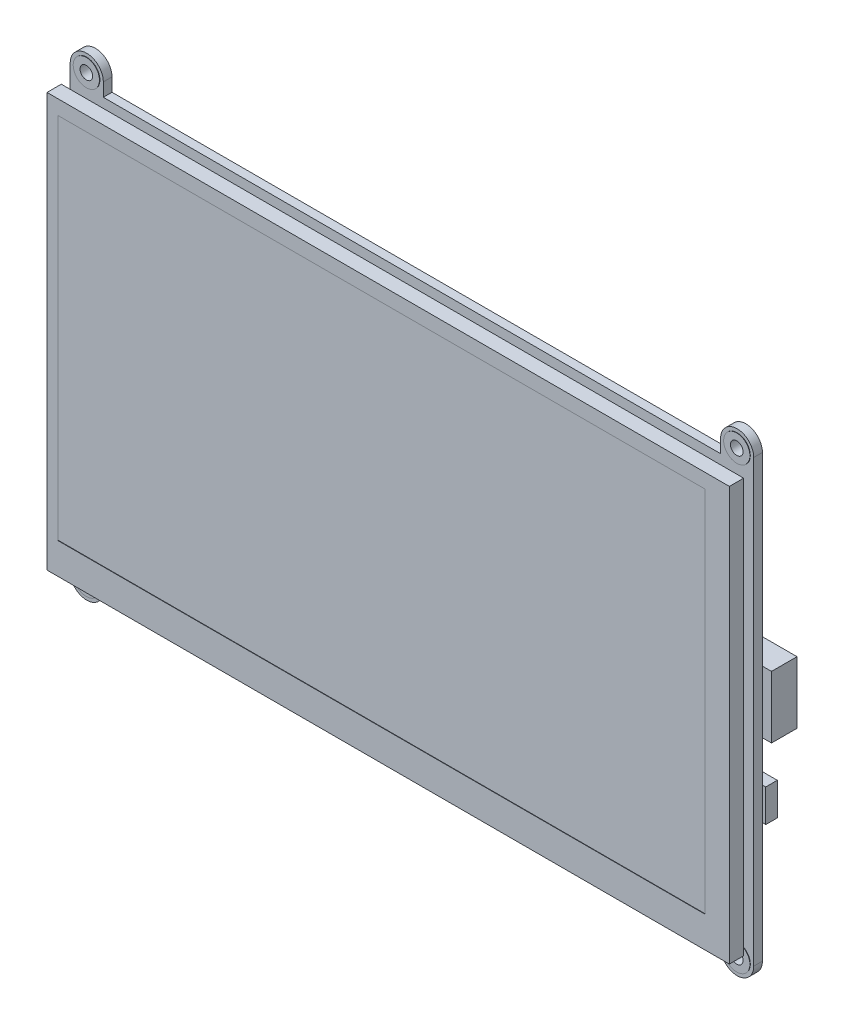
SolidWorks part; units mm, degrees
ref_plane "Plan de face" through (0, 0, 0) normal (0, 0, 1) x (1, 0, 0)
ref_plane "Plan de dessus" through (0, 0, 0) normal (0, 1, 0) x (1, 0, 0)
ref_plane "Plan de droite" through (0, 0, 0) normal (1, 0, 0) x (0, 0, -1)
sketch "Esquisse1" plane through (0, 0, 0) normal (0, 0, 1) x (1, 0, 0)
  line L0 (82.615, 53.25) -> (-82.615, -53.25) construction
  line L1 (0, 50.0368) -> (0, -50.0368) construction
  line L2 (-82.615, 53.25) -> (-82.615, -53.25)
  line L3 (-74.611, 50.0368) -> (74.611, 50.0368)
  line L4 (82.615, 53.25) -> (82.615, -53.25)
  line L5 (-78.613, 50.0368) -> (-78.613, 53.25) construction
  line L7 (-74.611, 50.0368) -> (-74.611, 53.25)
  line L8 (78.613, 50.0368) -> (78.613, 53.25) construction
  line L9 (74.611, 50.0368) -> (74.611, 53.25)
  line L11 (78.613, -50.0368) -> (78.613, -53.25) construction
  line L13 (74.611, -50.0368) -> (74.611, -53.25)
  line L14 (-78.613, -50.0368) -> (-78.613, -53.25) construction
  line L15 (-74.611, -50.0368) -> (-74.611, -53.25)
  line L17 (-74.611, -50.0368) -> (74.611, -50.0368)
  circle A0 centre (-78.613, 53.25) radius 1.524
  arc A1 (-74.611, 53.25) -> (-82.615, 53.25) centre (-78.613, 53.25) ccw
  circle A2 centre (-78.613, -53.25) radius 1.524
  arc A3 (82.615, 53.25) -> (74.611, 53.25) centre (78.613, 53.25) ccw
  circle A4 centre (78.613, -53.25) radius 1.524
  arc A5 (74.611, -53.25) -> (82.615, -53.25) centre (78.613, -53.25) ccw
  circle A6 centre (78.613, 53.25) radius 1.524
  arc A7 (-82.615, -53.25) -> (-74.611, -53.25) centre (-78.613, -53.25) ccw
  point P7 (-78.613, 53.25)
  point P12 (78.613, 51.625)
  point P21 (78.613, -51.625)
  point P28 (-78.613, -51.625)
  dimension "D5" = 3.048
  dimension "D1" = 100.0736
  dimension "D2" = 165.23
  dimension "D3" = 106.5
  dimension "D4" = 157.226
extrude "Boss.-Extru.1" add sketch "Esquisse1" along normal blind 2.1
sketch "Esquisse2" plane through (0, 0, 2.1) normal (0, 0, 1) x (1, 0, 0)
  line L0 (-74.5, 40) -> (74.5, -40) construction
  line L1 (-74.5, 40) -> (-49.1, 40)
  line L2 (-74.5, 40) -> (-74.5, 14.6)
  line L3 (-74.5, 14.6) -> (-49.1, 14.6)
  line L4 (-49.1, 40) -> (-49.1, 14.6)
  line L5 (-74.5, -14.6) -> (-49.1, -14.6)
  line L6 (-74.5, -14.6) -> (-74.5, -40)
  line L7 (-74.5, -40) -> (-49.1, -40)
  line L8 (-49.1, -14.6) -> (-49.1, -40)
  line L9 (49.1, 40) -> (74.5, 40)
  line L10 (49.1, 40) -> (49.1, 14.6)
  line L11 (49.1, 14.6) -> (74.5, 14.6)
  line L12 (74.5, 40) -> (74.5, 14.6)
  line L13 (49.1, -14.6) -> (74.5, -14.6)
  line L14 (49.1, -14.6) -> (49.1, -40)
  line L15 (49.1, -40) -> (74.5, -40)
  line L16 (74.5, -14.6) -> (74.5, -40)
  line L17 (-74.5, -40) -> (74.5, 40) construction
  dimension "D1" = 25.4
  dimension "D2" = 149
  dimension "D3" = 80
extrude "Boss.-Extru.2" add sketch "Esquisse2" along normal blind 2.3
sketch "Esquisse3" plane through (0, 0, 4.4) normal (0, 0, 1) x (1, 0, 0)
  line L1 (82.475, -50) -> (-82.475, -50)
  line L2 (82.475, -50) -> (82.475, 50)
  line L3 (82.475, 50) -> (-82.475, 50)
  line L4 (-82.475, -50) -> (-82.475, 50)
  line L5 (82.475, -50) -> (-82.475, 50) construction
  line L6 (82.475, 50) -> (-82.475, -50) construction
  point P0 (0, 0)
  dimension "D1" = 100
  dimension "D2" = 164.95
extrude "Boss.-Extru.3" add sketch "Esquisse3" along normal blind 3.45
sketch "Esquisse4" plane through (0, 0, 7.85) normal (0, 0, 1) x (1, 0, 0)
  line L0 (-82.475, 50) -> (-82.475, -50) construction
  line L1 (-79.855, 46.5) -> (76.645, 46.5)
  line L2 (-79.855, 46.5) -> (-79.855, -42.5)
  line L3 (-79.855, -42.5) -> (76.645, -42.5)
  line L4 (76.645, 46.5) -> (76.645, -42.5)
  line L5 (82.475, 50) -> (-82.475, 50) construction
  dimension "D1" = 156.5
  dimension "D2" = 2.62
  dimension "D3" = 3.5
  dimension "D4" = 89
extrude "Enlèv. mat.-Extru.1" cut sketch "Esquisse4" against normal blind 0.1
sketch "Esquisse5" plane through (0, 0, 0) normal (0, 0, -1) x (-1, 0, 0)
  line L0 (74.611, -50.0368) -> (-74.611, -50.0368) construction
  line L1 (23.415, 3.5632) -> (53.215, 3.5632)
  line L2 (23.415, 3.5632) -> (23.415, -3.8368)
  line L3 (23.415, -3.8368) -> (53.215, -3.8368)
  line L4 (53.215, 3.5632) -> (53.215, -3.8368)
  line L5 (82.615, 53.25) -> (82.615, -53.25) construction
  dimension "D1" = 29.8
  dimension "D2" = 7.4
  dimension "D3" = 46.2
  dimension "D4" = 29.4
extrude "Enlèv. mat.-Extru.2" cut sketch "Esquisse5" against normal blind 2.1
fillet "Congé1" radius 1 4 edges at (-23.415, 3.5632, 1.05) (-23.415, -3.8368, 1.05) (-53.215, -3.8368, 1.05) (-53.215, 3.5632, 1.05)
sketch "Esquisse6" plane through (0, 0, 0) normal (0, 0, -1) x (-1, 0, 0)
  line L0 (38.315, -3.8368) -> (38.315, 9.0632) construction
  line L1 (25.065, 9.0632) -> (51.565, 9.0632)
  line L2 (25.065, 9.0632) -> (25.065, 3.6632)
  line L3 (25.065, 3.6632) -> (51.565, 3.6632)
  line L4 (51.565, 9.0632) -> (51.565, 3.6632)
  line L5 (24.415, -3.8368) -> (52.215, -3.8368) construction
  line L7 (52.215, 3.5632) -> (24.415, 3.5632) construction
  dimension "D1" = 26.5
  dimension "D2" = 5.4
  dimension "D3" = 0.1
extrude "Boss.-Extru.4" add sketch "Esquisse6" along normal blind 2
sketch "Esquisse7" plane through (0, 0, 0) normal (0, 0, -1) x (-1, 0, 0)
  line L0 (-84.815, 1.0172) -> (-98.2984, 1.0172) construction
  line L1 (-84.815, 8.5172) -> (-73.225, 8.5172)
  line L2 (-84.815, 8.5172) -> (-84.815, -6.4828)
  line L3 (-84.815, -6.4828) -> (-73.225, -6.4828)
  line L4 (-73.225, 8.5172) -> (-73.225, -6.4828)
  line L5 (74.611, -50.0368) -> (-74.611, -50.0368) construction
  line L6 (-82.615, -53.25) -> (-82.615, 53.25) construction
  dimension "D1" = 51.054
  dimension "D2" = 15
  dimension "D3" = 11.59
  dimension "D4" = 2.2
extrude "Boss.-Extru.5" add sketch "Esquisse7" along normal blind 6.16
sketch "Esquisse8" plane through (0, 0, 0) normal (0, 0, -1) x (-1, 0, 0)
  line L0 (-83.415, -20.3188) -> (-92.7236, -20.3188) construction
  line L1 (-83.415, -16.3788) -> (-77.915, -16.3788)
  line L2 (-83.415, -16.3788) -> (-83.415, -24.2588)
  line L3 (-83.415, -24.2588) -> (-77.915, -24.2588)
  line L4 (-77.915, -16.3788) -> (-77.915, -24.2588)
  line L5 (74.611, -50.0368) -> (-74.611, -50.0368) construction
  line L6 (-82.615, -53.25) -> (-82.615, -6.4828) construction
  dimension "D2" = 7.88
  dimension "D3" = 5.5
  dimension "D4" = 0.8
extrude "Boss.-Extru.6" add sketch "Esquisse8" along normal blind 2.8
sketch "Esquisse9" plane through (0, 0, 0) normal (0, 0, -1) x (-1, 0, 0)
  line L0 (-74.611, 50.0368) -> (74.611, 50.0368) construction
  line L1 (-59.615, 7.5368) -> (-45.775, 7.5368)
  line L2 (-59.615, 7.5368) -> (-59.615, -6.3032)
  line L3 (-59.615, -6.3032) -> (-45.775, -6.3032)
  line L4 (-45.775, 7.5368) -> (-45.775, -6.3032)
  line L5 (-82.615, 8.5172) -> (-82.615, 53.25) construction
  dimension "D1" = 13.84
  dimension "D2" = 42.5
  dimension "D3" = 23
extrude "Boss.-Extru.7" add sketch "Esquisse9" along normal blind 1
sketch "Esquisse10" plane through (0, 0, 2.1) normal (0, 0, 1) x (1, 0, 0)
  circle A0 centre (-78.613, 53.25) radius 1.524
  circle A1 centre (-78.613, 53.25) radius 3.175
  circle A2 centre (-78.613, -53.25) radius 1.524
  circle A3 centre (-78.613, -53.25) radius 3.175
  circle A4 centre (78.613, -53.25) radius 1.524
  circle A5 centre (78.613, -53.25) radius 3.175
  circle A6 centre (78.613, 53.25) radius 1.524
  circle A7 centre (78.613, 53.25) radius 3.175
  circle A8 centre (78.613, 53.25) radius 1.524 construction
  circle A9 centre (-78.613, 53.25) radius 1.524 construction
  circle A10 centre (-78.613, -53.25) radius 1.524 construction
  circle A11 centre (78.613, -53.25) radius 1.524 construction
  dimension "D1" = 6.35
extrude "Boss.-Extru.8" add sketch "Esquisse10" along normal blind 0.1 and the other way blind 2.11
